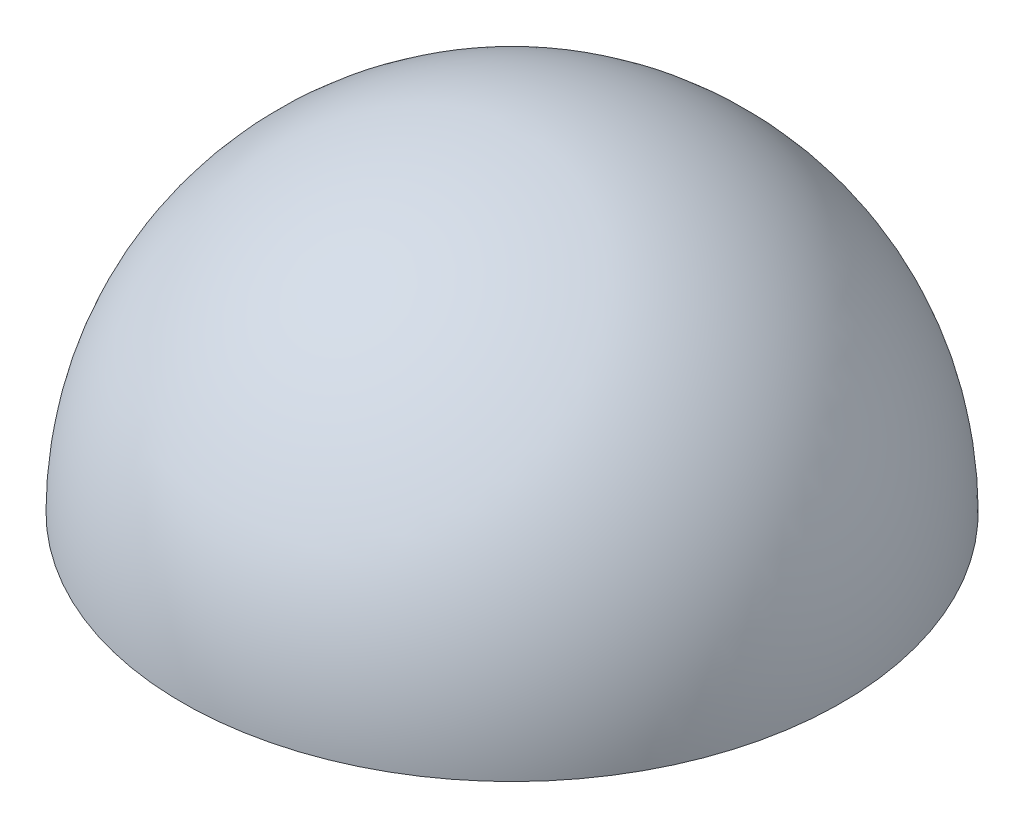
SolidWorks part; units mm, degrees
ref_plane "Front Plane" through (0, 0, 0) normal (0, 0, 1) x (1, 0, 0)
ref_plane "Top Plane" through (0, 0, 0) normal (0, 1, 0) x (1, 0, 0)
ref_plane "Right Plane" through (0, 0, 0) normal (1, 0, 0) x (0, 0, -1)
sketch "Sketch1" plane through (0, 0, 0) normal (1, 0, 0) x (0, 0, -1)
  line L0 (-7.0336, -54.9663) -> (-2.0336, -54.9663)
  line L1 (-7.0336, -54.9663) -> (-7.0336, -49.9663)
  arc A0 (-7.0336, -49.9663) -> (-2.0336, -54.9663) centre (-7.0336, -54.9663) cw
revolve "Revolve1" add sketch "Sketch1" angle 360 about L1
